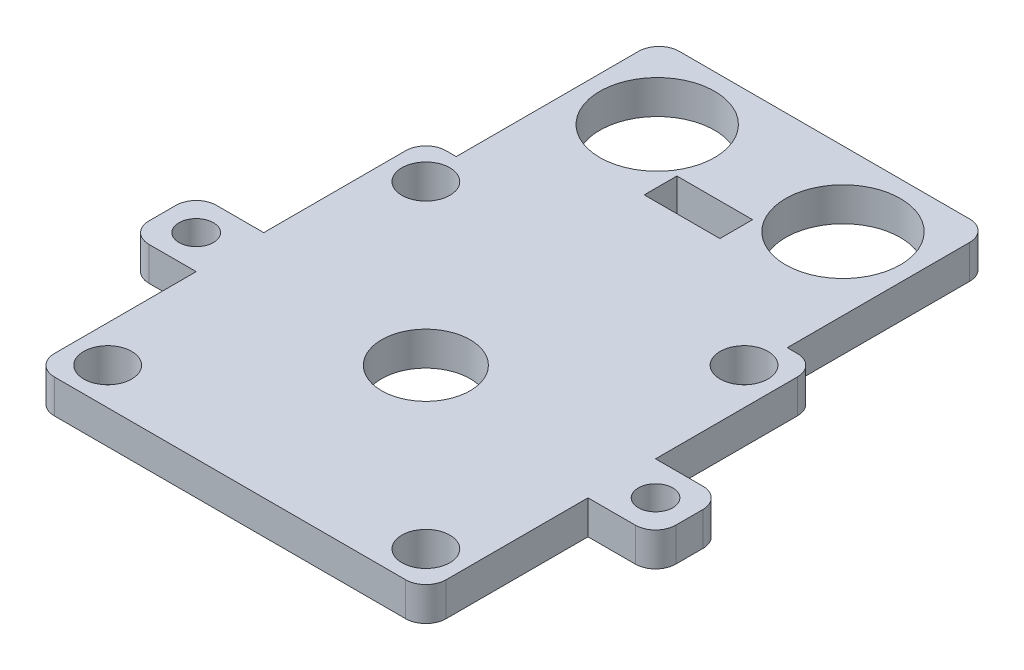
SolidWorks part; units mm, degrees
ref_plane "Front Plane" through (0, 0, 0) normal (0, 0, 1) x (1, 0, 0)
ref_plane "Top Plane" through (0, 0, 0) normal (0, 1, 0) x (1, 0, 0)
ref_plane "Right Plane" through (0, 0, 0) normal (1, 0, 0) x (0, 0, -1)
sketch "Sketch1" plane through (0, 0, 0) normal (0, 1, 0) x (1, 0, 0)
  circle A0 centre (0, 0) radius 20
  circle A1 centre (0, 0) radius 21
  dimension "D1" = 40
  dimension "D2" = 42
extrude "Boss-Extrude1" add sketch "Sketch1" along normal blind 3.5
ref_plane "Plane1" through (0, 3.5, 0) normal (0, 1, 0) x (1, 0, 0)
sketch "Sketch2" plane through (0, 3.5, 0) normal (0, 1, 0) x (1, 0, 0)
  line L0 (-23.55, 0) -> (23.55, 0) construction
  line L1 (-29, -29) -> (29, -29)
  line L2 (-29, -29) -> (-29, 29)
  line L3 (-29, 29) -> (29, 29)
  line L4 (29, -29) -> (29, 29)
  line L5 (-29, -29) -> (29, 29) construction
  line L6 (-29, 29) -> (29, -29) construction
  line L7 (-28.2, -28.2) -> (28.2, -28.2) construction
  line L8 (-28.2, -28.2) -> (-28.2, 28.2) construction
  line L9 (-28.2, 28.2) -> (28.2, 28.2) construction
  line L10 (28.2, -28.2) -> (28.2, 28.2) construction
  line L11 (-28.2, -28.2) -> (28.2, 28.2) construction
  line L12 (-28.2, 28.2) -> (28.2, -28.2) construction
  line L13 (-23.55, 28.2) -> (-23.55, 23.55) construction
  line L14 (-23.55, 23.55) -> (-28.2, 23.55) construction
  line L15 (0, 28.2) -> (0, -28.2) construction
  line L16 (0, 29) -> (0, 49) construction
  line L17 (-22.5, 49) -> (22.5, 49) construction
  line L18 (-22.5, 49) -> (-22.5, 29) construction
  line L19 (22.5, 49) -> (22.5, 29) construction
  line L20 (0, 49) -> (0, 48) construction
  line L21 (-4.9, 48) -> (4.9, 48) construction
  line L22 (-4.9, 48) -> (-4.9, 44.56) construction
  line L23 (-4.9, 44.56) -> (4.9, 44.56) construction
  line L24 (4.9, 44.56) -> (4.9, 48) construction
  line L25 (-24.5, 29) -> (-24.5, 51)
  line L26 (-24.5, 51) -> (24.5, 51)
  line L27 (24.5, 51) -> (24.5, 29)
  line L28 (-13.76, 39) -> (13.76, 39) construction
  line L29 (-5.6, 48.7) -> (5.6, 48.7)
  line L31 (5.6, 43.86) -> (-5.6, 43.86)
  line L32 (-5.6, 43.86) -> (-5.6, 48.7)
  line L33 (5.6, 43.86) -> (5.6, 48.7)
  line L34 (-24.5, 51) -> (-24.5, 59)
  line L35 (-24.5, 59) -> (24.5, 59)
  line L36 (24.5, 59) -> (24.5, 51)
  line L37 (0, 0) -> (34, 0) construction
  line L38 (29, 5) -> (39, 5)
  line L39 (29, -5) -> (39, -5)
  line L40 (39, 5) -> (39, -5)
  line L41 (-29, -5) -> (-39, -5)
  line L42 (-39, 5) -> (-39, -5)
  line L43 (-29, 5) -> (-39, 5)
  circle A0 centre (-23.55, 23.55) radius 2.55 construction
  circle A1 centre (23.55, 23.55) radius 2.55 construction
  circle A2 centre (23.55, -23.55) radius 2.55 construction
  circle A3 centre (-23.55, -23.55) radius 2.55 construction
  circle A4 centre (0, 0) radius 5.5563 construction
  circle A5 centre (13.76, 39) radius 7.5 construction
  circle A6 centre (-13.76, 39) radius 7.5 construction
  circle A7 centre (-13.76, 39) radius 8.5
  circle A8 centre (13.76, 39) radius 8.5
  circle A9 centre (0, 0) radius 6.55
  circle A10 centre (-23.55, 23.55) radius 3.55
  circle A11 centre (23.55, 23.55) radius 3.55
  circle A12 centre (23.55, -23.55) radius 3.55
  circle A13 centre (-23.55, -23.55) radius 3.55
  circle A14 centre (34, 0) radius 2.55
  circle A15 centre (-34, 0) radius 2.55
  point P0 (0, 0)
  point P5 (0, 0)
  point P15 (0, 0)
  point P34 (0, 49)
  point P40 (0, 48)
  point P49 (0, 39)
  point P56 (0, 43.86)
  point P59 (0, 48.7)
  point P70 (34, 0)
  dimension "D4" = 5.1
  dimension "D5" = 11.1125
  dimension "D15" = 15
  dimension "D16" = 17
  dimension "D17" = 0.7
  dimension "D20" = 13.1
  dimension "D21" = 7.1
  dimension "D22" = 8
  dimension "D24" = 5.1
  dimension "D25" = 5
  dimension "D1" = 58
  dimension "D2" = 56.4
  dimension "D3" = 47.1
  dimension "D6" = 20
  dimension "D7" = 45
  dimension "D8" = 1
  dimension "D9" = 9.8
  dimension "D10" = 3.44
  dimension "D11" = 2
  dimension "D12" = 2
  dimension "D13" = 2
  dimension "D14" = 27.52
  dimension "D18" = 0.7
  dimension "D19" = 0.7
  dimension "D23" = 34
  dimension "D26" = 5
extrude "Boss-Extrude2" add sketch "Sketch2" along normal blind 5 contours L1 L4 L3 L2 A4 A1 A0 A2 A3 | L27 L26 L25 L3 A8 A7 L33 L31 L32 L29 | L40 L38 L4 L39 A14 | L2 L43 L42 L41 A15
sketch "Sketch3" plane through (0, 3.5, 0) normal (0, 1, 0) x (1, 0, 0)
  line L0 (-5.6, 48.7) -> (5.6, 48.7)
  line L1 (5.6, 48.7) -> (5.6, 43.86)
  line L2 (5.6, 43.86) -> (-5.6, 43.86)
  line L3 (-5.6, 43.86) -> (-5.6, 48.7)
  line L4 (-13.76, 47.5) -> (-13.76, 30.5) construction
  line L5 (13.76, 47.5) -> (13.76, 30.5) construction
  line L6 (-24.5, 29) -> (24.5, 29)
  line L7 (24.5, 29) -> (24.5, 51)
  line L8 (24.5, 51) -> (-24.5, 51)
  line L9 (-24.5, 51) -> (-24.5, 29)
  line L10 (-24.5, 51) -> (-24.5, 59)
  line L11 (-24.5, 59) -> (24.5, 59)
  line L12 (24.5, 59) -> (24.5, 51)
  circle A0 centre (-13.76, 39) radius 8.5 construction
  circle A1 centre (-13.76, 39) radius 8.5
  circle A2 centre (13.76, 39) radius 8.5 construction
  circle A3 centre (13.76, 39) radius 8.5
  dimension "D1" = 8
sketch "Sketch4" plane through (0, 3.5, 0) normal (0, 1, 0) x (1, 0, 0)
  line L4 (-5.6791, 42.84) -> (-5.6791, 38)
  line L5 (5.5209, 38) -> (5.5209, 42.84)
  line L10 (-24.5, 29) -> (-24.5, 37)
  line L11 (-24.5, 51) -> (-24.5, 29) construction
  line L12 (24.5, 29) -> (24.5, 37)
  line L13 (24.5, 29) -> (24.5, 51) construction
  line L14 (-24.5, 37) -> (-24.5, 59)
  line L15 (24.5, 37) -> (24.5, 59)
  line L16 (-24.5, 59) -> (24.5, 59)
  line L17 (-24.5, 37) -> (24.5, 37)
  line L18 (0, 59) -> (0, 37) construction
  line L23 (-5.6791, 38) -> (5.5209, 38)
  line L24 (5.5209, 42.84) -> (-5.6791, 42.84)
  line L25 (-5.6791, 58) -> (5.5209, 58) construction
  line L26 (5.5209, 58) -> (5.5209, 53.16) construction
  line L27 (5.5209, 53.16) -> (-5.6791, 53.16) construction
  line L28 (-5.6791, 53.16) -> (-5.6791, 58) construction
  line L29 (-13.75, 56.5) -> (-13.75, 39.5) construction
  line L30 (-13.75, 48) -> (13.75, 48) construction
  circle A4 centre (-13.75, 48) radius 8.5
  circle A5 centre (13.75, 48) radius 8.5
  point P53 (0, 48)
  dimension "D2" = 17
  dimension "D1" = 8
  dimension "D3" = 22
  dimension "D4" = 1
  dimension "D5" = 5.5209
  dimension "D6" = 11.2
  dimension "D7" = 4.84
  dimension "D8" = 27.5
extrude "Ignore" add sketch "Sketch3" along normal blind 5 contours L3 L2 L1 L0 | L12 L11 L10 L8 | A3 | A1
extrude "Cut-Extrude2" cut sketch "Sketch4" along normal through all contours A4 | A5 | L28 L27 L26 L25 | L5 L24 L4 L23
fillet "Fillet1" radius 3 10 edges at (29, 6, -29) (39, 6, 5) (39, 6, -5) (29, 6, 29) (-29, 6, 29) (-39, 6, 5) (-39, 6, -5) (-29, 6, -29) (24.5, 6, -59) (-24.5, 6, -59)
